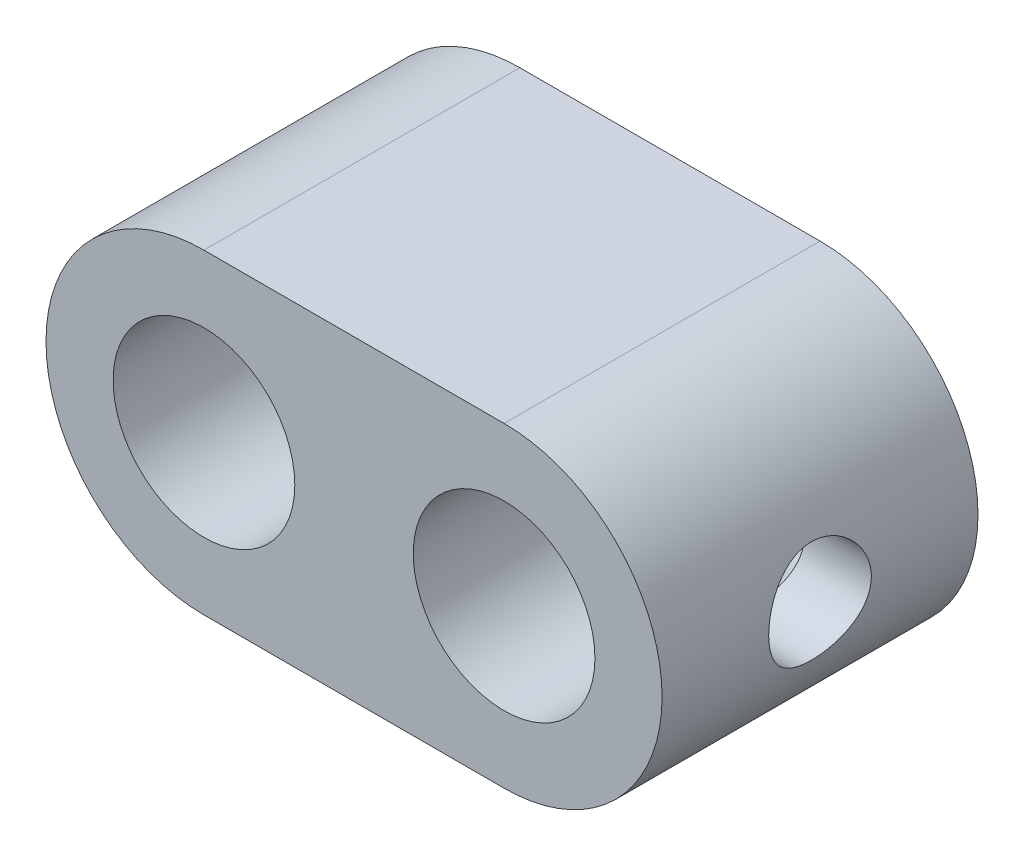
SolidWorks part; units mm, degrees
ref_plane "Front Plane" through (0, 0, 0) normal (0, 0, 1) x (1, 0, 0)
ref_plane "Top Plane" through (0, 0, 0) normal (0, 1, 0) x (1, 0, 0)
ref_plane "Right Plane" through (0, 0, 0) normal (1, 0, 0) x (0, 0, -1)
sketch "Sketch1" plane through (0, 0, 0) normal (0, 0, 1) x (1, 0, 0)
  line L0 (0, 0) -> (-9.5, 0) construction
  line L1 (0, -5) -> (-9.5, -5)
  line L2 (0, 5) -> (-9.5, 5)
  circle A0 centre (0, 0) radius 2.875
  arc A2 (0, -5) -> (0, 5) centre (0, 0) ccw
  arc A3 (-9.5, 5) -> (-9.5, -5) centre (-9.5, 0) ccw
  circle A4 centre (-9.5, 0) radius 2.875
  point P3 (-4.75, 0)
  dimension "D1" = 5.75
  dimension "D2" = 5
  dimension "D3" = 5.75
  dimension "D4" = 9.5
extrude "Boss-Extrude1" add sketch "Sketch1" along normal blind 10
sketch "Sketch2" plane through (0, 0, 0) normal (1, 0, 0) x (0, 0, -1)
  line L0 (-5, 0) -> (0, 0) construction
  circle A0 centre (-5, 0) radius 1.625
  dimension "D1" = 3.25
  dimension "D2" = 5
extrude "Cut-Extrude1" cut sketch "Sketch2" against normal through all both and the other way through all
